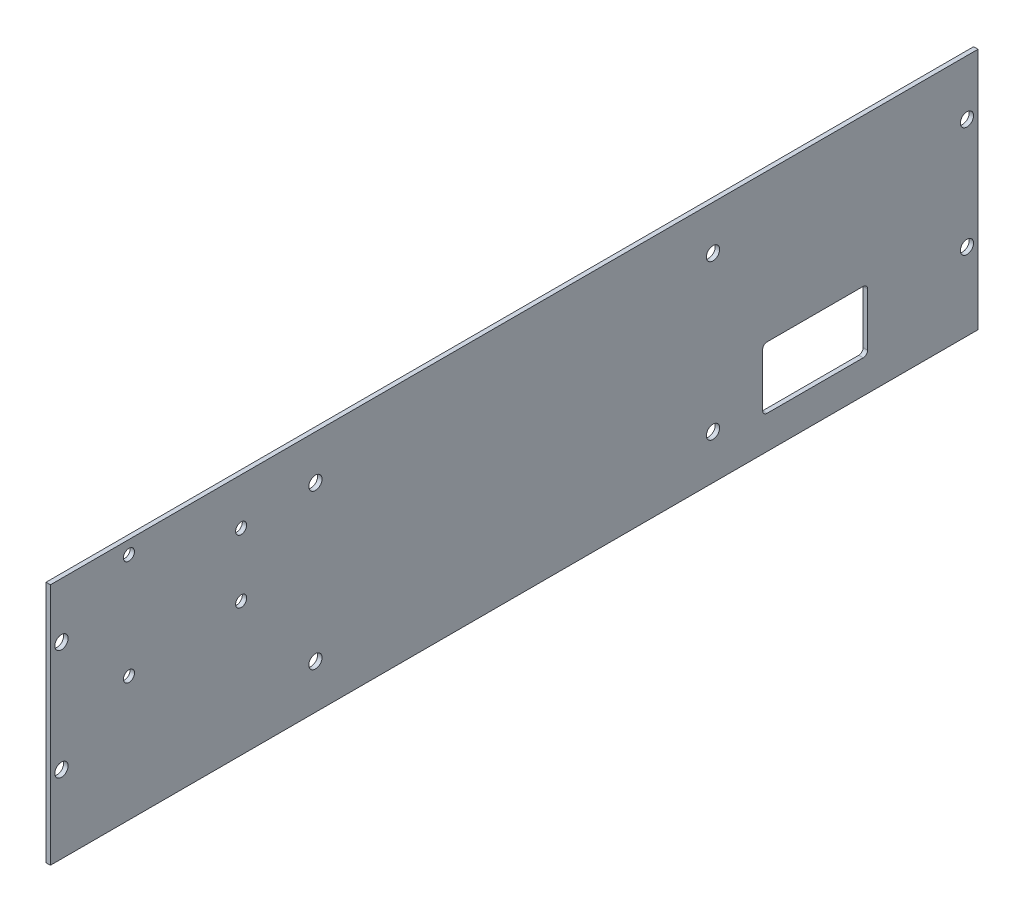
SolidWorks part; units mm, degrees
ref_plane "Front Plane" through (0, 0, 0) normal (0, 0, 1) x (1, 0, 0)
ref_plane "Top Plane" through (0, 0, 0) normal (0, 1, 0) x (1, 0, 0)
ref_plane "Right Plane" through (0, 0, 0) normal (1, 0, 0) x (0, 0, -1)
sketch "Sketch1" plane through (-26.0517, 0, 0) normal (-1, 0, 0) x (0, 0, 1)
  line L0 (410.1922, -10) -> (-40.8078, -10) construction
  line L1 (394.6922, 100) -> (-25.3078, 100)
  line L2 (394.6922, 100) -> (394.6922, -10)
  line L3 (394.6922, -10) -> (-25.3078, -10)
  line L4 (-25.3078, 100) -> (-25.3078, -10)
  line L5 (414.6922, -10) -> (414.6922, 0) construction
  dimension "D1" = 20
  dimension "D2" = 110
extrude "Boss-Extrude1" add sketch "Sketch1" along normal blind 2
sketch "Sketch2" plane through (-28.0517, 0, 0) normal (-1, 0, 0) x (0, 0, 1)
  circle A0 centre (-20.3078, 75) radius 3
  circle A1 centre (-20.3078, 25) radius 3
  circle A2 centre (389.6922, 75) radius 3
  circle A3 centre (389.6922, 25) radius 3
  dimension "D1" = 6
extrude "Cut-Extrude1" cut sketch "Sketch2" against normal up to next
sketch "Sketch3" plane through (-28.0517, 0, 0) normal (-1, 0, 0) x (0, 0, 1)
  line L0 (-25.3078, -10) -> (394.6922, -10) construction
  line L1 (24.6922, 33) -> (72.1922, 33)
  line L2 (24.6922, 33) -> (24.6922, 5)
  line L3 (24.6922, 5) -> (72.1922, 5)
  line L4 (72.1922, 33) -> (72.1922, 5)
  line L5 (-25.3078, 100) -> (-25.3078, -10) construction
  circle A0 centre (94.6922, 10) radius 3
  circle A1 centre (274.6922, 10) radius 3
  circle A2 centre (94.6922, 80) radius 3
  circle A3 centre (274.6922, 80) radius 3
  circle A4 centre (359.1226, 94) radius 2.5
  circle A5 centre (308.3226, 79) radius 2.5
  circle A6 centre (308.3226, 50.4) radius 2.5
  circle A7 centre (359.1226, 46.4) radius 2.5
  dimension "D1" = 5
  dimension "D2" = 5
  dimension "D3" = 5
  dimension "D4" = 5
  dimension "D5" = 47.5
  dimension "D6" = 28
  dimension "D7" = 15
  dimension "D8" = 50
extrude "Cut-Extrude2" cut sketch "Sketch3" against normal up to next
fillet "Fillet1" radius 2 4 edges at (-27.0517, 5, 72.1922) (-27.0517, 33, 72.1922) (-27.0517, 5, 24.6922) (-27.0517, 33, 24.6922)
